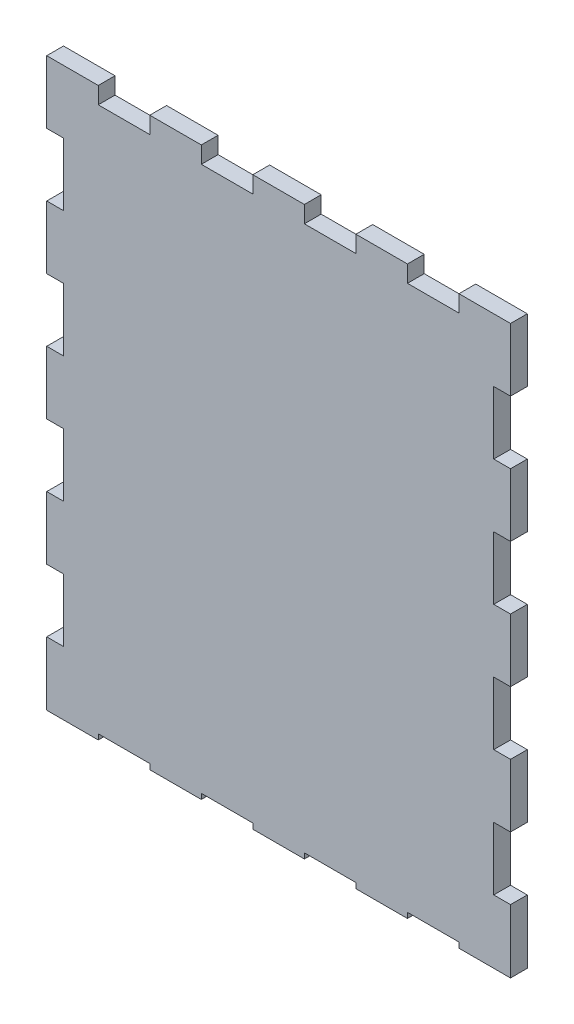
SolidWorks part; units mm, degrees
ref_plane "Front Plane" through (0, 0, 0) normal (0, 0, 1) x (1, 0, 0)
ref_plane "Top Plane" through (0, 0, 0) normal (0, 1, 0) x (1, 0, 0)
ref_plane "Right Plane" through (0, 0, 0) normal (1, 0, 0) x (0, 0, -1)
sketch "Sketch2" plane through (0, 0, 0) normal (0, 0, 1) x (1, 0, 0)
  line L0 (-68.58, -83.82) -> (68.58, 83.82) construction
  line L1 (-68.58, -83.82) -> (68.58, -83.82)
  line L2 (-68.58, -83.82) -> (-68.58, 83.82)
  line L3 (-68.58, 83.82) -> (68.58, 83.82)
  line L4 (68.58, -83.82) -> (68.58, 83.82)
  line L5 (68.58, -83.82) -> (-68.58, 83.82) construction
  point P0 (27.8435, 34.031)
  dimension "D2" = 137.16
  dimension "D3" = 167.64
extrude "Boss-Extrude1" add sketch "Sketch2" along normal blind 4.9609
sketch "Sketch3" plane through (0, 0, 4.9609) normal (0, 0, 1) x (1, 0, 0)
  line L20 (-68.58, 83.82) -> (-68.58, 65.2018) construction
  line L21 (-68.58, -83.82) -> (68.58, -83.82) construction
  line L22 (-68.58, 27.9908) -> (-68.58, 9.398)
  line L23 (-68.58, 65.2018) -> (-63.619, 65.2018)
  line L24 (-68.58, 65.2018) -> (-68.58, 46.609)
  line L25 (-68.58, 46.609) -> (-63.619, 46.609)
  line L26 (-63.619, 65.2018) -> (-63.619, 46.609)
  line L27 (-68.58, 27.9908) -> (-63.619, 27.9908)
  line L28 (-63.619, 27.9908) -> (-63.619, 9.398)
  line L29 (-68.58, 9.398) -> (-63.619, 9.398)
  line L30 (-68.58, -9.2202) -> (-68.58, -27.813)
  line L31 (-68.58, -9.2202) -> (-63.619, -9.2202)
  line L32 (-63.619, -9.2202) -> (-63.619, -27.813)
  line L33 (-68.58, -27.813) -> (-63.619, -27.813)
  line L34 (-68.58, -46.4312) -> (-68.58, -65.024)
  line L35 (-68.58, -46.4312) -> (-63.619, -46.4312)
  line L36 (-63.619, -46.4312) -> (-63.619, -65.024)
  line L37 (-68.58, -65.024) -> (-63.619, -65.024)
  line L38 (-68.58, 83.82) -> (-53.34, 83.82) construction
  line L39 (-63.619, 46.609) -> (-63.619, 27.9908) construction
  line L60 (-68.58, 83.82) -> (-68.58, -83.82) construction
  line L61 (68.58, 83.82) -> (68.58, 65.2018) construction
  line L62 (68.58, 83.82) -> (-68.58, 83.82) construction
  line L63 (68.58, 27.9908) -> (68.58, 9.398)
  line L64 (68.58, 65.2018) -> (63.619, 65.2018)
  line L65 (68.58, 65.2018) -> (68.58, 46.609)
  line L66 (68.58, 46.609) -> (63.619, 46.609)
  line L67 (63.619, 65.2018) -> (63.619, 46.609)
  line L68 (68.58, 27.9908) -> (63.619, 27.9908)
  line L69 (63.619, 27.9908) -> (63.619, 9.398)
  line L70 (68.58, 9.398) -> (63.619, 9.398)
  line L71 (68.58, -9.2202) -> (68.58, -27.813)
  line L72 (68.58, -9.2202) -> (63.619, -9.2202)
  line L73 (63.619, -9.2202) -> (63.619, -27.813)
  line L74 (68.58, -27.813) -> (63.619, -27.813)
  line L75 (68.58, -46.4312) -> (68.58, -65.024)
  line L76 (68.58, -46.4312) -> (63.619, -46.4312)
  line L77 (63.619, -46.4312) -> (63.619, -65.024)
  line L78 (68.58, -65.024) -> (63.619, -65.024)
  line L79 (63.619, 46.609) -> (63.619, 27.9908) construction
  line L80 (-22.86, 83.82) -> (-22.86, 78.859)
  line L81 (-53.34, 83.82) -> (-38.1, 83.82)
  line L82 (-53.34, 83.82) -> (-53.34, 78.859)
  line L83 (-53.34, 78.859) -> (-38.1, 78.859)
  line L84 (-38.1, 83.82) -> (-38.1, 78.859)
  line L85 (-22.86, 83.82) -> (-7.62, 83.82)
  line L86 (-7.62, 83.82) -> (-7.62, 78.859)
  line L87 (-22.86, 78.859) -> (-7.62, 78.859)
  line L88 (7.62, 83.82) -> (7.62, 78.859)
  line L89 (7.62, 83.82) -> (22.86, 83.82)
  line L90 (22.86, 83.82) -> (22.86, 78.859)
  line L91 (7.62, 78.859) -> (22.86, 78.859)
  line L92 (38.1, 83.82) -> (38.1, 78.859)
  line L93 (38.1, 83.82) -> (53.34, 83.82)
  line L94 (53.34, 83.82) -> (53.34, 78.859)
  line L95 (38.1, 78.859) -> (53.34, 78.859)
  line L96 (-38.1, 83.82) -> (-22.86, 83.82) construction
  line L97 (-68.58, -83.82) -> (-53.34, -83.82) construction
  line L98 (-38.1, 78.859) -> (-22.86, 78.859) construction
  line L99 (-22.86, -83.82) -> (-22.86, -82.2325)
  line L100 (-53.34, -83.82) -> (-38.1, -83.82)
  line L101 (-53.34, -83.82) -> (-53.34, -82.2325)
  line L102 (-53.34, -82.2325) -> (-38.1, -82.2325)
  line L103 (-38.1, -83.82) -> (-38.1, -82.2325)
  line L104 (-22.86, -83.82) -> (-7.62, -83.82)
  line L105 (-7.62, -83.82) -> (-7.62, -82.2325)
  line L106 (-22.86, -82.2325) -> (-7.62, -82.2325)
  line L107 (7.62, -83.82) -> (7.62, -82.2325)
  line L108 (7.62, -83.82) -> (22.86, -83.82)
  line L109 (22.86, -83.82) -> (22.86, -82.2325)
  line L110 (7.62, -82.2325) -> (22.86, -82.2325)
  line L111 (38.1, -83.82) -> (38.1, -82.2325)
  line L112 (38.1, -83.82) -> (53.34, -83.82)
  line L113 (53.34, -83.82) -> (53.34, -82.2325)
  line L114 (38.1, -82.2325) -> (53.34, -82.2325)
  line L115 (-38.1, -82.2325) -> (-22.86, -82.2325) construction
  dimension "D2" = 15.24
  dimension "D4" = 18.6182
  dimension "D5" = 15.24
  dimension "D6" = 15.24
  dimension "D10" = 4
  dimension "D13" = 15.24
  dimension "D14" = 1.5875
  dimension "D15" = 18.5928
  dimension "D18" = 18.6182
  dimension "D3" = 4.961
  dimension "D12" = 18.6182
  dimension "D7" = 4
  dimension "D17" = 4
  dimension "D20" = 4
extrude "Cut-Extrude1" cut sketch "Sketch3" against normal through all
